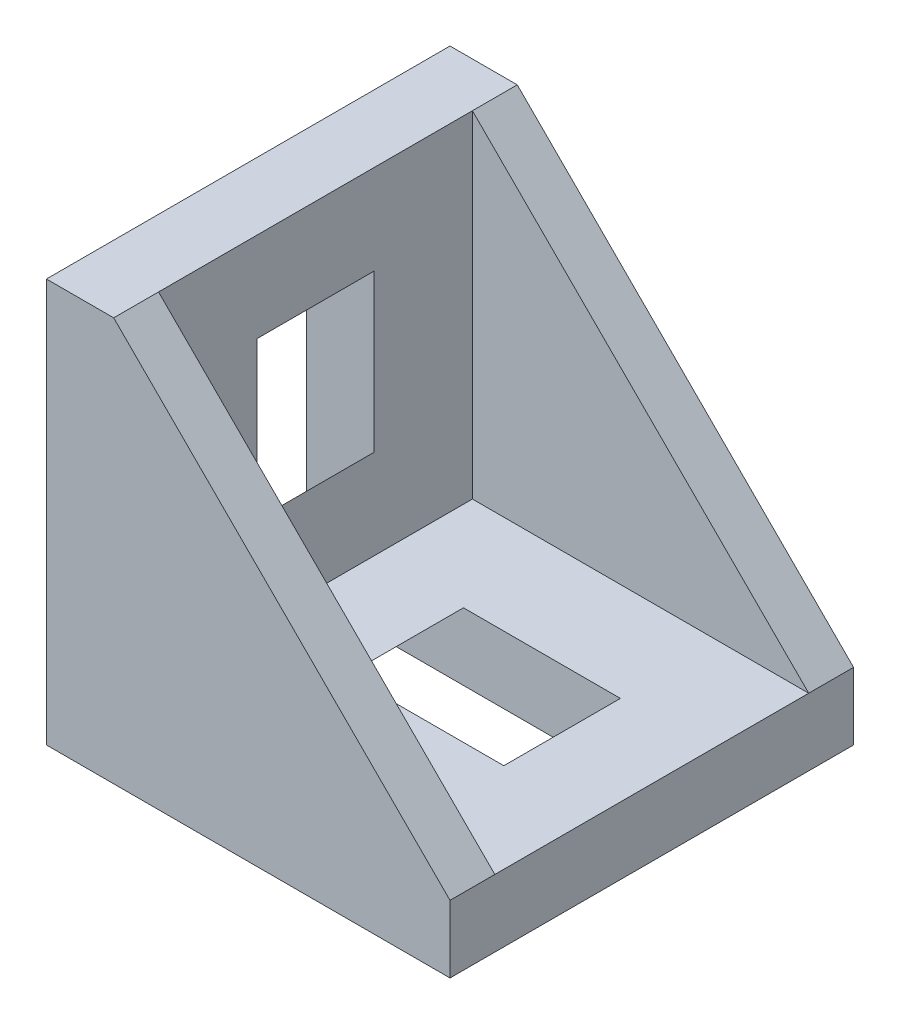
SolidWorks part; units mm, degrees
ref_plane "Front Plane" through (0, 0, 0) normal (0, 0, 1) x (1, 0, 0)
ref_plane "Top Plane" through (0, 0, 0) normal (0, 1, 0) x (1, 0, 0)
ref_plane "Right Plane" through (0, 0, 0) normal (1, 0, 0) x (0, 0, -1)
sketch "Sketch1" plane through (0, 0, 0) normal (0, 0, 1) x (1, 0, 0)
  line L0 (0, 0) -> (0, 18)
  line L1 (18, 3) -> (3, 18)
  line L4 (3, 18) -> (0, 18)
  line L5 (18, 0) -> (0, 0)
  line L7 (18, 3) -> (18, 0)
  dimension "D" = 3
  dimension "C" = 18
  dimension "B" = 18
extrude "Boss-Extrude1" add sketch "Sketch1" along normal mid plane 18
sketch "Sketch2" plane through (0, 0, 0) normal (0, 0, 1) x (1, 0, 0)
  line L0 (3, 18) -> (3, 3)
  line L1 (3, 3) -> (18, 3)
  line L2 (3, 18) -> (18, 3)
extrude "Cut-Extrude1" cut sketch "Sketch2" against normal mid plane 14
sketch "Sketch3" plane through (0, 0, 0) normal (0, 0, 1) x (1, 0, 0)
  line L0 (18, 3) -> (3, 18) construction
  line L1 (0, 14) -> (3, 14)
  line L2 (0, 14) -> (0, 4)
  line L3 (0, 4) -> (3, 7)
  line L4 (3, 14) -> (3, 7)
  line L5 (7, 3) -> (14, 3)
  line L6 (7, 3) -> (4, 0)
  line L7 (4, 0) -> (14, 0)
  line L8 (14, 3) -> (14, 0)
  line L10 (18, 0) -> (0, 0) construction
  line L11 (0, 0) -> (0, 18) construction
  dimension "D1" = 14
  dimension "D2" = 7
  dimension "D3" = 14
  dimension "D4" = 7
extrude "Cut-Extrude2" cut sketch "Sketch3" against normal mid plane 5.2
sketch "Sketch4" plane through (0, 0, 0) normal (0, 0, 1) x (1, 0, 0)
  line L0 (0, 18) -> (0, 0) construction
  line L1 (1.2115, 2.3429) -> (0, 1.2348) construction
  line L2 (1.4975, -1.8063) -> (0.5049, -0.7979)
  line L3 (0, 3.5355) -> (-1.8063, 1.4975)
  line L4 (-1.8063, 1.4975) -> (-0.7979, 0.5049)
  line L5 (-0.7979, 0.5049) -> (0, 1.2348)
  line L6 (0, 1.2348) -> (0, 3.5355)
  line L7 (0.5049, -0.7979) -> (1.2348, 0)
  line L8 (0, 0) -> (0, 18) construction
  line L9 (-1.3021, 1.0012) -> (0, 2.3239) construction
  line L10 (1.2348, 0) -> (3.5355, 0)
  line L11 (3.5355, 0) -> (1.4975, -1.8063)
  line L12 (0, 17.3) -> (0, 14.9992)
  line L13 (0, 14.9992) -> (-0.7979, 14.2693)
  line L14 (-0.7979, 14.2693) -> (-1.8063, 15.2619)
  line L15 (-1.8063, 15.2619) -> (0, 17.3)
  line L16 (-1.3021, 14.7656) -> (0, 16.0884) construction
  line L17 (0, 16.0884) -> (0.6057, 16.7037) construction
  line L18 (18, 3) -> (3, 18) construction
  line L19 (10.5, 10.5) -> (0, 0) construction
  line L20 (0, 17.3) -> (1.2115, 16.1074) construction
  line L21 (0, 14.9992) -> (1.2115, 16.1074) construction
  line L22 (0, 3.5355) -> (1.2115, 2.3429) construction
  line L23 (14.9992, 0) -> (14.2693, -0.7979)
  line L24 (0.6057, 2.9392) -> (0, 2.3239) construction
  line L25 (14.2693, -0.7979) -> (15.2619, -1.8063)
  line L26 (17.3, 0) -> (14.9992, 0)
  line L27 (15.2619, -1.8063) -> (17.3, 0)
  line L28 (-1.8063, 1.4975) -> (-1.8063, 15.2619) construction
  dimension "D1" = 1.7
  dimension "D2" = 5
  dimension "D3" = 6
  dimension "D4" = 1.6001
  dimension "D5" = 0.7
  dimension "D6" = 0.2
extrude "Boss-Extrude2" add sketch "Sketch4" along normal mid plane 6
